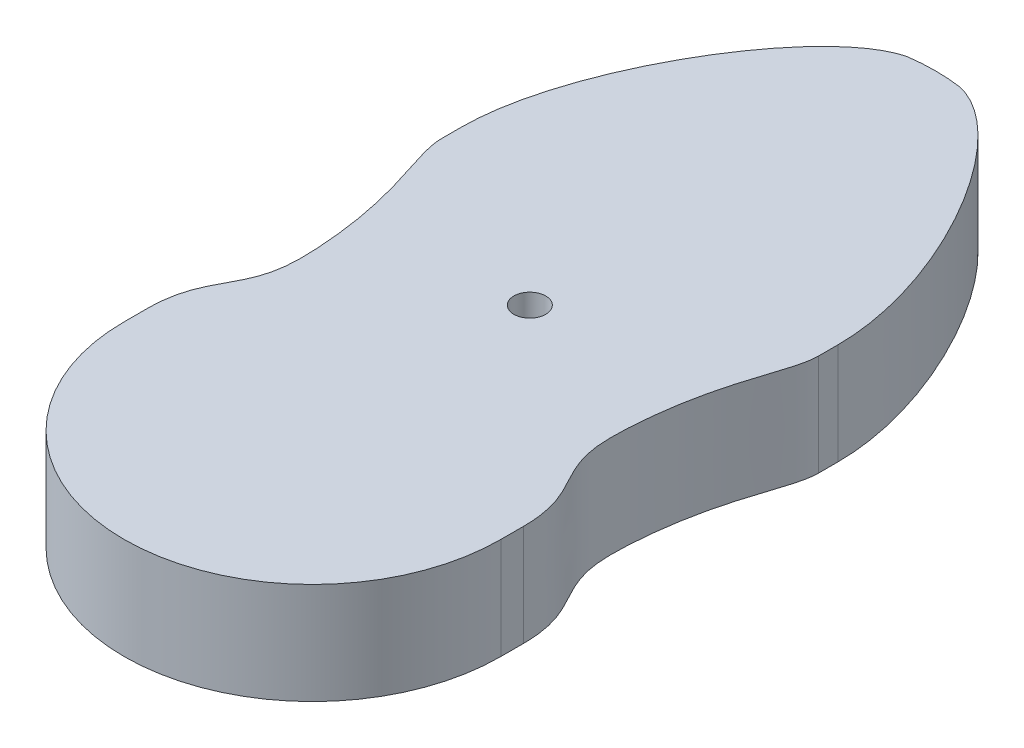
SolidWorks part; units mm, degrees
material "POLYURETHANE (11671)"
ref_plane "Front Plane" through (0, 0, 0) normal (0, 0, 1) x (1, 0, 0)
ref_plane "Top Plane" through (0, 0, 0) normal (0, 1, 0) x (1, 0, 0)
ref_plane "Right Plane" through (0, 0, 0) normal (1, 0, 0) x (0, 0, -1)
sketch "Sketch1" plane through (0, 0, 0) normal (0, 1, 0) x (1, 0, 0)
  line L0 (0, 75) -> (0, -75) construction
  line L1 (65, 75) -> (65, -75)
  line L2 (-65, 75) -> (-65, -75)
  line L3 (-65, 73.2915) -> (-65, 9.3349) construction
  line L4 (17.6904, 139.7446) -> (-29.2088, 139.7446) construction
  line L5 (-65, 23.45) -> (-65, 45.6788) construction
  line L6 (-65, -78.5921) -> (-65, -55.7623) construction
  line L7 (-53.5279, -33.8769) -> (-53.5279, 1.2492) construction
  line L8 (0, 140) -> (0, -140) construction
  line L9 (-65, 41.3132) -> (-65, 34.5644)
  arc A0 (65, 75) -> (-65, 75) centre (0, 75) ccw
  arc A1 (-65, -75) -> (65, -75) centre (0, -75) ccw
  spline S0 degree 3 poles (-65, 34.5644) (-65, 25.3044) (-54.8759, 10.0009) (-52.5082, -44.6661) (-65, -48.3308) (-65, -67.1772) knots 0 0 0 0 0.557561 0.657561 1 1 1 1
  spline S1 degree 3 poles (-65, 41.3132) (-65, 81.2861) (-28.4072, 139.7446) (-5.7559, 139.7446) knots 0 0 0 0 1 1 1 1
  spline S2 degree 3 poles (65, 41.3132) (65, 81.2861) (28.4072, 139.7446) (5.7559, 139.7446) knots 0 0 0 0 1 1 1 1
  spline S3 degree 3 poles (65, 34.5644) (65, 25.3044) (54.8759, 10.0009) (52.5082, -44.6661) (65, -48.3308) (65, -67.1772) knots 0 0 0 0 0.557561 0.657561 1 1 1 1
  point P2 (0, 0)
  point P33 (0, 5)
  dimension "D2" = 280
  dimension "D3" = 149.8567
  dimension "D4" = 62.8212
  dimension "D5" = 30.8664
  dimension "D6" = 119.9186
  dimension "D7" = 67.9539
  dimension "D1" = 130
  dimension "D8" = 53.5279
  dimension "D9" = 145
extrude "Boss-Extrude1" add sketch "Sketch1" along normal blind 35 contours S3 L1 S2 A0 S1 L2 S0 A1
hole_wizard "M10 Clearance Hole1" positions "Sketch2" profile "Sketch3" hole size "M10" standard "ANSI Metric" end condition through all
sketch "Sketch2" plane through (0, 35, 0) normal (0, 1, 0) x (1, 0, 0)
  point P0 (0, 0)
sketch "Sketch3" plane through (0, 35, 0) normal (1, 0, 0) x (0, 0, 1)
  line L0 (0, 0) -> (0, 35)
  line L1 (0, 35) -> (5.5, 35)
  line L2 (5.5, 35) -> (5.5, 0)
  line L5 (5.5, 0) -> (0, 0)
  line L11 (0, -6.35) -> (0, 107.95) construction
  dimension "Thru Hole Dia." = 11
  dimension "Thru Hole Depth" = 35
